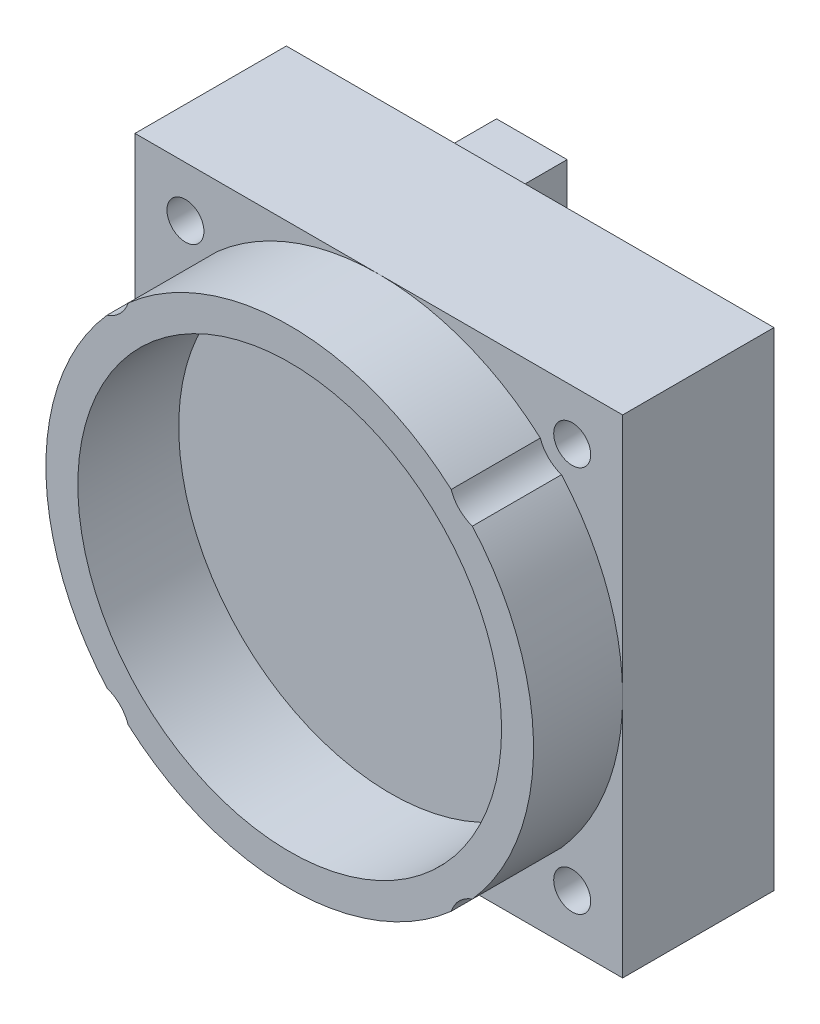
SolidWorks part; units mm, degrees
ref_plane "Front Plane" through (0, 0, 0) normal (0, 0, 1) x (1, 0, 0)
ref_plane "Top Plane" through (0, 0, 0) normal (0, 1, 0) x (1, 0, 0)
ref_plane "Right Plane" through (0, 0, 0) normal (1, 0, 0) x (0, 0, -1)
sketch "Sketch1" plane through (0, 0, 0) normal (0, 0, 1) x (1, 0, 0)
  line L1 (0, 0) -> (29, 0)
  line L2 (0, 0) -> (0, 29)
  line L3 (0, 29) -> (29, 29)
  line L4 (29, 0) -> (29, 29)
  dimension "D1" = 29
  dimension "D2" = 29
extrude "Boss-Extrude1" add sketch "Sketch1" along normal blind 9
sketch "Sketch3" plane through (0, 0, 9) normal (0, 0, 1) x (1, 0, 0)
  line L0 (0, 29) -> (29, 0) construction
  circle A0 centre (14.5, 14.5) radius 14.5
  dimension "D1" = 29
extrude "Boss-Extrude2" add sketch "Sketch3" along normal blind 5.3 contours A0
sketch "Sketch4" plane through (0, 0, 14.3) normal (0, 0, 1) x (1, 0, 0)
  circle A0 centre (14.5, 14.5) radius 12.6
  circle A1 centre (14.5, 14.5) radius 14.5 construction
  dimension "D1" = 1.9
extrude "Cut-Extrude1" cut sketch "Sketch4" against normal blind 6
sketch "Sketch5" plane through (0, 0, 0) normal (0, 0, -1) x (-1, 0, 0)
  line L0 (-29, 14.5) -> (0, 14.5) construction
  line L1 (0, 29) -> (0, 0) construction
  line L2 (-14.5, 29) -> (-14.5, 14.5) construction
  circle A0 centre (-26, 26) radius 1.1
  circle A1 centre (-3, 26) radius 1.1
  circle A2 centre (-3, 3) radius 1.1
  circle A3 centre (-26, 3) radius 1.1
  dimension "D1" = 2.2
  dimension "D2" = 11.5
  dimension "D3" = 11.5
extrude "Cut-Extrude2" cut sketch "Sketch5" against normal through all
sketch "Sketch6" plane through (0, 0, 9) normal (0, 0, 1) x (1, 0, 0)
  line L0 (14.5, 29) -> (14.5, 0) construction
  line L1 (0, 14.5) -> (29, 14.5) construction
  circle A0 centre (3, 26) radius 2
  circle A1 centre (14.5, 14.5) radius 14.5 construction
  circle A2 centre (26, 26) radius 2
  circle A3 centre (26, 3) radius 2
  circle A4 centre (3, 3) radius 2
  dimension "D1" = 4
extrude "Cut-Extrude3" cut sketch "Sketch6" along normal through all
sketch "Sketch7" plane through (0, 0, 0) normal (0, 0, -1) x (-1, 0, 0)
  line L0 (-29, 29) -> (0, 29) construction
  line L1 (-28, 28) -> (-1, 28)
  line L2 (-28, 28) -> (-28, 1)
  line L3 (-28, 1) -> (-1, 1)
  line L4 (-1, 28) -> (-1, 21)
  line L5 (-29, 0) -> (-29, 29) construction
  line L6 (0, 0) -> (-29, 0) construction
  line L7 (0, 29) -> (0, 0) construction
  line L8 (-1, 21) -> (-5.65, 21)
  line L9 (-5.65, 21) -> (-5.65, 8)
  line L10 (-5.65, 8) -> (-1, 8)
  line L11 (-28, 14.5) -> (-5.65, 14.5) construction
  line L12 (-1, 8) -> (-1, 1)
  circle A0 centre (-26, 3) radius 1.1 construction
  circle A1 centre (-3, 3) radius 1.1 construction
  circle A2 centre (-3, 26) radius 1.1 construction
  circle A3 centre (-26, 26) radius 1.1 construction
  circle A4 centre (-26, 3) radius 1.1
  circle A5 centre (-3, 3) radius 1.1
  circle A6 centre (-3, 26) radius 1.1
  circle A7 centre (-26, 26) radius 1.1
  dimension "D1" = 1
  dimension "D2" = 1
  dimension "D3" = 1
  dimension "D4" = 1
  dimension "D5" = 13
  dimension "D6" = 4.65
  dimension "D7" = 6.5
extrude "Boss-Extrude3" add sketch "Sketch7" along normal blind 0.5
sketch "Sketch8" plane through (0, 0, 0) normal (0, 0, -1) x (-1, 0, 0)
  circle A0 centre (-26, 26) radius 2
  circle A1 centre (-3, 26) radius 2
  circle A2 centre (-26, 3) radius 2
  circle A3 centre (-3, 3) radius 2
  circle A4 centre (-3, 3) radius 1.1 construction
  circle A5 centre (-26, 3) radius 1.1 construction
  circle A6 centre (-3, 26) radius 1.1 construction
  circle A7 centre (-26, 26) radius 1.1 construction
  circle A8 centre (-3, 3) radius 1.1
  circle A9 centre (-26, 3) radius 1.1
  circle A10 centre (-3, 26) radius 1.1
  circle A11 centre (-26, 26) radius 1.1
  dimension "D1" = 4
  dimension "D2" = 4
  dimension "D3" = 4
  dimension "D4" = 4
extrude "Boss-Extrude4" add sketch "Sketch8" along normal blind 1 separate body
sketch "Sketch9" plane through (0, 0, 0) normal (0, 0, -1) x (-1, 0, 0)
  line L0 (0, 29) -> (0, 0) construction
  line L1 (0, 21) -> (-5.65, 21)
  line L2 (0, 21) -> (0, 8)
  line L3 (0, 8) -> (-5.65, 8)
  line L4 (-5.65, 21) -> (-5.65, 8)
  line L5 (-29, 14.5) -> (0, 14.5) construction
  dimension "D1" = 13
  dimension "D2" = 6.5
  dimension "D3" = 5.65
extrude "Boss-Extrude5" add sketch "Sketch9" along normal blind 3.3 separate body
sketch "Sketch10" plane through (0, 0, 0) normal (-1, 0, 0) x (0, 0, 1)
  line L0 (-3.3, 8) -> (0, 8) construction
  line L1 (-2.8, 20.5) -> (-0.5, 20.5)
  line L2 (-2.8, 20.5) -> (-2.8, 16)
  line L3 (-2.8, 16) -> (-0.5, 16)
  line L4 (-0.5, 20.5) -> (-0.5, 16)
  line L5 (-2.8, 15.5) -> (-0.5, 15.5)
  line L6 (-2.8, 15.5) -> (-2.8, 8.5)
  line L7 (-2.8, 8.5) -> (-0.5, 8.5)
  line L8 (-0.5, 15.5) -> (-0.5, 8.5)
  line L9 (-3.3, 8) -> (-3.3, 21) construction
  line L10 (0, 29) -> (0, 0) construction
  line L11 (-3.3, 21) -> (0, 21) construction
  dimension "D1" = 0.5
  dimension "D2" = 0.5
  dimension "D3" = 0.5
  dimension "D4" = 0.5
  dimension "D5" = 0.5
  dimension "D6" = 4.5
extrude "Cut-Extrude4" cut sketch "Sketch10" against normal blind 3.3
sketch "Sketch11" plane through (0, 0, -0.5) normal (0, 0, -1) x (-1, 0, 0)
  line L0 (0, 29) -> (0, 0) construction
  line L1 (-7, 26) -> (-11.2, 26)
  line L2 (-7, 26) -> (-7, 22.8)
  line L3 (-7, 22.8) -> (-11.2, 22.8)
  line L4 (-11.2, 26) -> (-11.2, 22.8)
  line L5 (-29, 29) -> (0, 29) construction
  dimension "D1" = 4.2
  dimension "D2" = 3.2
  dimension "D3" = 7
  dimension "D4" = 3
extrude "Boss-Extrude6" add sketch "Sketch11" along normal blind 5
sketch "Sketch12" plane through (0, 0, -0.5) normal (0, 0, -1) x (-1, 0, 0)
  line L0 (-7, 26) -> (-11.2, 26) construction
  line L1 (-15.2, 26) -> (-22.2, 26)
  line L2 (-15.2, 26) -> (-15.2, 19)
  line L3 (-15.2, 19) -> (-22.2, 19)
  line L4 (-22.2, 26) -> (-22.2, 19)
  line L5 (-22.2, 16) -> (-12.2, 16)
  line L6 (-22.2, 16) -> (-22.2, 6)
  line L7 (-22.2, 6) -> (-12.2, 6)
  line L8 (-12.2, 16) -> (-12.2, 6)
  line L9 (-11.2, 26) -> (-11.2, 22.8) construction
  dimension "D1" = 7
  dimension "D2" = 7
  dimension "D3" = 4
  dimension "D4" = 10
  dimension "D5" = 10
  dimension "D6" = 3
extrude "Boss-Extrude7" add sketch "Sketch12" along normal blind 0.5
